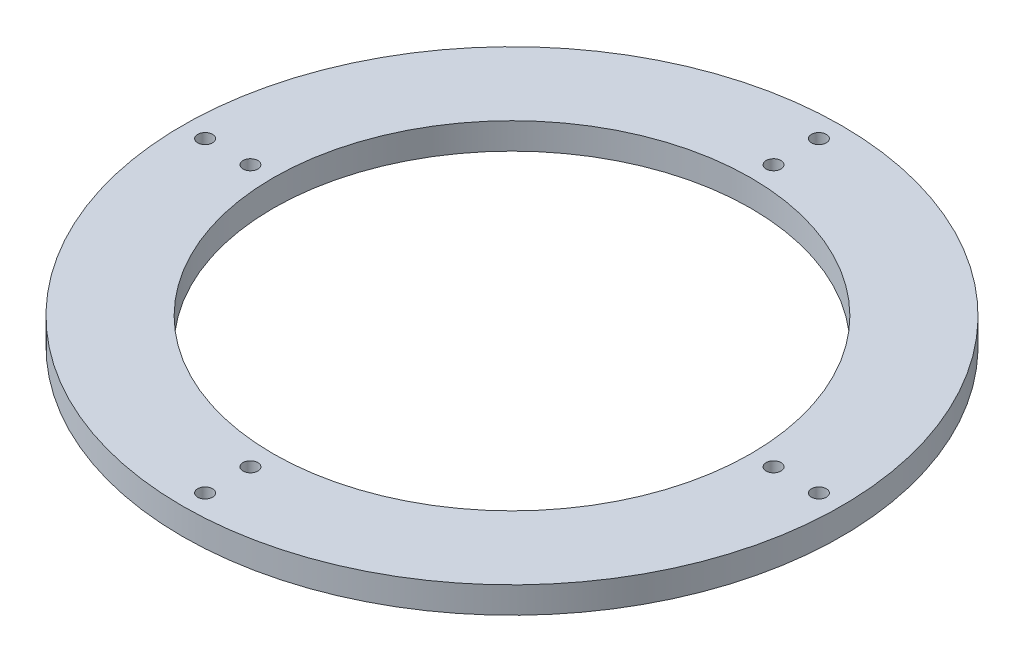
SolidWorks part; units mm, degrees
ref_plane "Front Plane" through (0, 0, 0) normal (0, 0, 1) x (1, 0, 0)
ref_plane "Top Plane" through (0, 0, 0) normal (0, 1, 0) x (1, 0, 0)
ref_plane "Right Plane" through (0, 0, 0) normal (1, 0, 0) x (0, 0, -1)
sketch "Sketch1" plane through (0, 0, 0) normal (0, 1, 0) x (1, 0, 0)
  circle A0 centre (0, 0) radius 100
  circle A1 centre (0, 0) radius 72.5
  dimension "D1" = 200
  dimension "D2" = 145
extrude "Boss-Extrude1" add sketch "Sketch1" along normal blind 8
sketch "Sketch2" plane through (0, 0, 0) normal (0, 1, 0) x (1, 0, 0)
  circle A0 centre (0, 93.125) radius 2.25
  circle A1 centre (93.125, 0) radius 2.25
  circle A2 centre (0, -93.125) radius 2.25
  circle A3 centre (-93.125, 0) radius 2.25
  circle A4 centre (0, 79.375) radius 2.25
  circle A5 centre (79.375, 0) radius 2.25
  circle A6 centre (0, -79.375) radius 2.25
  circle A7 centre (-79.375, 0) radius 2.25
  circle A8 centre (0, 0) radius 86.25 construction
  point P12 (0, 0)
  point P21 (0, 0)
  dimension "D1" = 4.5
  dimension "D2" = 93.125
  dimension "D4" = 4.5
  dimension "D5" = 79.375
  dimension "D6" = 4
  dimension "D7" = 172.5
  dimension "D3" = 4
extrude "Cut-Extrude1" cut sketch "Sketch2" along normal blind 8
